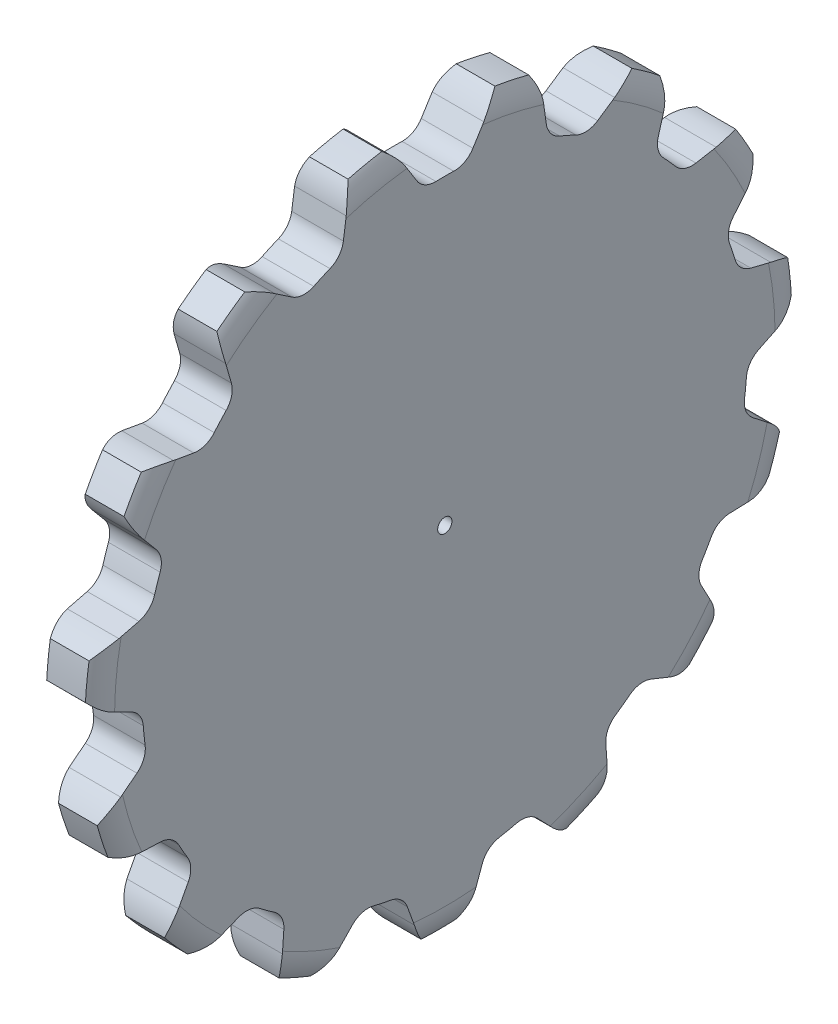
SolidWorks part; units mm, degrees
ref_plane "Plane1" through (0, 0, 0) normal (0, 0, 1) x (1, 0, 0)
ref_plane "Plane2" through (0, 0, 0) normal (0, 1, 0) x (1, 0, 0)
ref_plane "Plane3" through (0, 0, 0) normal (1, 0, 0) x (0, 0, -1)
sketch "Clipboard" plane through (0, 0, 0) normal (0, 1, 0) x (1, 0, 0)
  line L0 (0, 0) -> (22.1792, -5.9429)
  line L1 (-15, 0) -> (100, 0) construction
  line L2 (0, 0) -> (-2.1039, 2.3779)
  line L3 (0, 0) -> (-11.863, 4.5341)
  line L4 (0, 0) -> (8.3417, 2.2352)
  line L5 (0, 0) -> (-47.5972, -17.7524)
  line L6 (0, 0) -> (-7.1589, -4.8301)
  line L7 (-2.1039, 2.3779) -> (8.8308, 51.9871)
  line L8 (-76.2, 54.61) -> (-73.5584, 54.61)
  line L9 (-71.009, 38.7566) -> (-66.7127, 40.3203)
  line L10 (-76.2, 71.12) -> (-20.9804, 71.12)
  circle A0 centre (0, 0) radius 7.9375
  circle A1 centre (0, 0) radius 38.1
  circle A2 centre (0, 0) radius 38.1
  dimension "MHD" = 76.2
  dimension "Hub_dia" = 76.2
  dimension "Num_teeth" = 15
  dimension "Pitch_radius" = 55.2196
  dimension "Pitch" = 22.9616
  dimension "Overall_len" = 50.8
  dimension "Show_teeth" = 15
  dimension "Thickness" = 8.636
  dimension "OAL" = 50.8001
  dimension "T_dim" = 2.6416
  dimension "Ap" = 20
  dimension "H" = 4.572
sketch "BasProSke" plane through (0, 0, 0) normal (0, 1, 0) x (1, 0, 0)
  line L0 (-10, 0) -> (60, 0) construction
  line L1 (0, 0) -> (0, 55.2196)
  line L2 (0, 0) -> (8.636, 0)
  line L3 (8.636, 0) -> (8.636, 55.2196)
  line L4 (7.5565, 59.1058) -> (1.0795, 59.1058)
  arc A0 (0, 55.2196) -> (1.0795, 59.1058) centre (7.5349, 55.2196) cw
  arc A1 (8.636, 55.2196) -> (7.5565, 59.1058) centre (1.1011, 55.2196) ccw
  dimension "D1" = 7.5349
  dimension "G1" = 1.0795
  dimension "G2" = 1.0795
  dimension "H2" = 3.8862
  dimension "Diameter" = 118.2116
  dimension "H1" = 3.8862
  dimension "Thickness" = 8.636
revolve "Base-Revolve" add sketch "BasProSke" angle 360 about L0
sketch "TooCutSke" plane through (0, 0, 0) normal (1, 0, 0) x (0, 0, -1)
  line L0 (-4.6978, 52.2606) -> (-6.523, 55.1815)
  line L1 (0, 0) -> (0, 107) construction
  line L2 (1.1481, 0) -> (1.1481, 288.74) construction
  line L3 (4.6978, 52.2606) -> (6.523, 55.1815)
  line L5 (1.1481, 58.5401) -> (43.6042, 32.0106) construction
  arc A0 (1.4883, 50.5429) -> (-1.4883, 50.5429) centre (0, 0) ccw
  arc A1 (1.4883, 50.5429) -> (4.6978, 52.2606) centre (1.596, 54.1989) ccw
  arc A2 (-1.4883, 50.5429) -> (-4.6978, 52.2606) centre (-1.596, 54.1989) cw
  circle A3 centre (0, 0) radius 55.2196 construction
  circle A4 centre (1.1481, 55.2077) radius 4.572 construction
  arc A5 (6.523, 55.1815) -> (12.7602, 60.0322) centre (16.2592, 49.0976) cw
  arc A6 (-6.523, 55.1815) -> (-12.7602, 60.0322) centre (-16.2592, 49.0976) ccw
  arc A7 (12.7602, 60.0322) -> (-12.7602, 60.0322) centre (0, 0) ccw
  dimension "R" = 3.6576
  dimension "Dr" = 50.5648
  dimension "H" = 4.572
  dimension "Pitch_radius" = 55.2196
  dimension "Rt" = 11.4808
  dimension "Ag" = 64
  dimension "Cp" = 1.1481
  dimension "L" = 3.4442
  dimension "Angle" = 24
extrude "ToothCut" cut sketch "TooCutSke" along normal through all
pattern_circular "TeethCuts" count 15 every 24 about axis through (-10, 0, 0) along (1, 0, 0) of "ToothCut"
sketch "HubNeaOneSke" plane through (0, 0, 0) normal (-1, 0, 0) x (0, 0, 1)
  circle A0 centre (0, 0) radius 38.1
  dimension "Diameter" = 76.2
extrude "HubNearOne" [suppressed] add sketch "HubNeaOneSke" along normal blind 42.1641
sketch "HubNeaBotSke" plane through (0, 0, 0) normal (-1, 0, 0) x (0, 0, 1)
  circle A0 centre (0, 0) radius 38.1
  dimension "Diameter" = 76.2
extrude "HubNearBoth" [suppressed] add sketch "HubNeaBotSke" along normal blind 21.082
ref_plane "FarPln" through (8.636, 0, 0) normal (1, 0, 0) x (0, 0, -1)
sketch "HubFarSke" plane through (8.636, 0, 0) normal (1, 0, 0) x (0, 0, -1)
  circle A0 centre (0, 0) radius 38.1
  dimension "Diameter" = 76.2
extrude "HubFar" [suppressed] add sketch "HubFarSke" along normal blind 21.082
sketch "BorSke" plane through (0, 0, 0) normal (1, 0, 0) x (0, 0, -1)
  circle A0 centre (0, 0) radius 1.1913
  dimension "Diameter" = 2.3825
extrude "Bore" cut sketch "BorSke" along normal mid plane 101.6001
sketch "KeySke" plane through (0, 0, 0) normal (1, 0, 0) x (0, 0, -1)
  line L0 (-0.127, 0) -> (-0.127, 1.4503)
  line L1 (-0.127, 1.4503) -> (0.127, 1.4503)
  line L2 (0.127, 1.4503) -> (0.127, 0)
  line L3 (0, 0) -> (0, 34) construction
  line L4 (-0.127, 0) -> (0.127, 0)
  dimension "Offset" = 1.4503
  dimension "Width" = 0.254
extrude "Keyway" [suppressed] cut sketch "KeySke" along normal mid plane 101.6001
pattern_circular "Keyway2" [suppressed] count 2 every 90 about axis through (-10, 0, 0) along (1, 0, 0)
equation "\"Num_teeth@Clipboard\" = int( \"Num_teeth@Clipboard\" )"
equation "\"Num_teeth@Clipboard\" = ((sgn( \"Num_teeth@Clipboard\" - 5.0)+1)*( \"Num_teeth@Clipboard\" - 5.0))/2 +5.0"
equation "' \"Num_teeth@Clipboard\" = ((sgn( \"Num_teeth@Clipboard\" - 200.0)-1)*( \"Num_teeth@Clipboard\" - 200.0))/-2 +200.0"
equation "\"OAL@Clipboard\" = \"Thickness@Clipboard\""
equation "\"Pitch_radius@Clipboard\" = ( \"Pitch@Clipboard\" / 2.0) / sin(3.14159265 / \"Num_teeth@Clipboard\" )"
equation "\"MHD@Clipboard\" =2.0 * ( \"Pitch_radius@Clipboard\" * 0.9985 -  \"H@Clipboard\" )"
equation "\"MHD@Clipboard\" = ((sgn( \"MHD@Clipboard\" - \"Hub_dia@Clipboard\" )-1)*( \"MHD@Clipboard\" - \"Hub_dia@Clipboard\" ))/-2+ \"Hub_dia@Clipboard\""
equation "\"OAL@Clipboard\" = ((sgn( \"OAL@Clipboard\" - \"Overall_len@Clipboard\" )+1)*( \"OAL@Clipboard\" - \"Overall_len@Clipboard\" ))/2 + \"Overall_len@Clipboard\" + 0.000002"
equation "\"Num_teeth@TeethCuts\" = int( \"Show_teeth@Clipboard\" ) + 1"
equation "\"Num_teeth@TeethCuts\" = ((sgn( \"Num_teeth@TeethCuts\" - \"Num_teeth@Clipboard\" )-1)*( \"Num_teeth@TeethCuts\" - \"Num_teeth@Clipboard\" ))/-2+ \"Num_teeth@Clipboard\""
equation "\"Num_teeth@TeethCuts\" = ((sgn( \"Num_teeth@TeethCuts\" - 2.0)+1)*( \"Num_teeth@TeethCuts\" - 2.0))/2 +2.0"
equation "\"Angle@TeethCuts\" = 360.0 / \"Num_teeth@Clipboard\""
equation "\"Pitch_radius@TooCutSke\" = \"Pitch_radius@Clipboard\""
equation "\"Cp@TooCutSke\" = 0.05 * \"Pitch@Clipboard\""
equation "\"Rt@TooCutSke\" = 0.5 * \"Pitch@Clipboard\""
equation "\"R@TooCutSke\"  = 0.8 * \"H@Clipboard\""
equation "\"Dr@TooCutSke\" = \"Pitch_radius@Clipboard\" * 0.9985 -  \"H@Clipboard\""
equation "\"Ag@TooCutSke\" =  2.0 * \"Ap@Clipboard\" + 360.0 / \"Num_teeth@Clipboard\""
equation "\"L@TooCutSke\" = 0.01 * \"Pitch@Clipboard\" * \"Num_teeth@Clipboard\""
equation "\"H@TooCutSke\" = \"H@Clipboard\""
equation "\"Angle@TooCutSke\" =  360.0 / \"Num_teeth@Clipboard\""
equation "\"Diameter@BasProSke\" = 2.0 * \"Pitch_radius@Clipboard\"  + 1.7 * \"H@Clipboard\""
equation "\"Thickness@BasProSke\"  = \"Thickness@Clipboard\""
equation "\"G1@BasProSke\" =  \"Thickness@Clipboard\" * 0.125"
equation "\"G2@BasProSke\" =   \"Thickness@Clipboard\" * 0.125"
equation "\"H1@BasProSke\" =  \"Diameter@BasProSke\" / 2.0 - \"Pitch_radius@Clipboard\""
equation "\"H2@BasProSke\" =  \"Diameter@BasProSke\" / 2.0 - \"Pitch_radius@Clipboard\""
equation "\"Diameter@HubNeaOneSke\" = \"MHD@Clipboard\""
equation "\"Length@HubNearOne\" = \"OAL@Clipboard\" - \"Thickness@BasProSke\""
equation "\"Diameter@HubNeaBotSke\" = \"MHD@Clipboard\""
equation "\"Length@HubNearBoth\" = ( \"OAL@Clipboard\" - \"Thickness@BasProSke\" ) / 2.0"
equation "\"Thickness@FarPln\" = \"Thickness@BasProSke\""
equation "\"Diameter@HubFarSke\" = \"MHD@Clipboard\""
equation "\"Length@HubFar\" = ( \"OAL@Clipboard\" - \"Thickness@BasProSke\" ) / 2.0"
equation "\"D1@Bore\" = \"OAL@Clipboard\" * 2.0"
equation "\"D1@Keyway\" = \"OAL@Clipboard\" * 2.0"
equation "\"Offset@KeySke\" = \"T_dim@Clipboard\" - \"Diameter@BorSke\" / 2.0"
